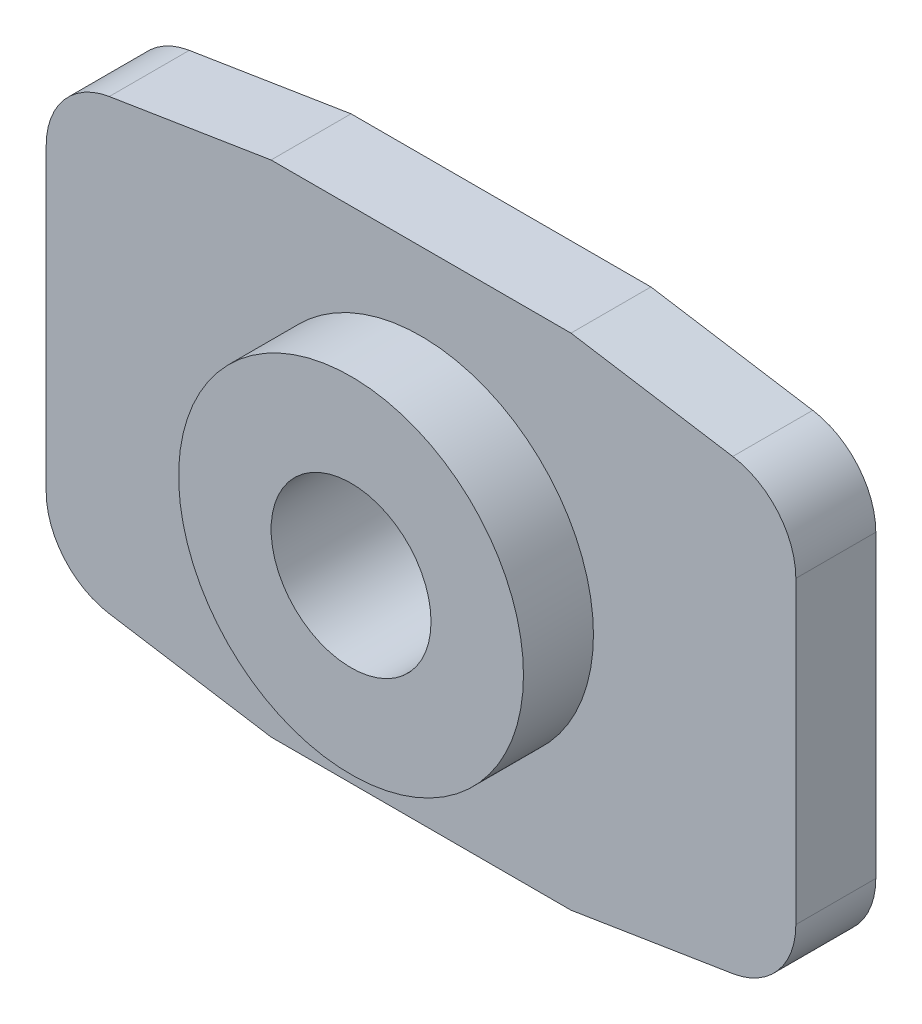
SolidWorks part; units mm, degrees
material "Plain Carbon Steel"
ref_plane "Front Plane" through (0, 0, 0) normal (0, 0, 1) x (1, 0, 0)
ref_plane "Top Plane" through (0, 0, 0) normal (0, 1, 0) x (1, 0, 0)
ref_plane "Right Plane" through (0, 0, 0) normal (1, 0, 0) x (0, 0, -1)
sketch "Sketch1" plane through (0, 0, 0) normal (0, 0, 1) x (1, 0, 0)
  line L0 (-7.5, 0) -> (7.5, 0) construction
  line L1 (-6.2374, 4.4811) -> (-3, 5)
  line L2 (-7.5, -3) -> (-7.5, 3)
  line L3 (-3, 5) -> (3, 5)
  line L4 (7.5, -3) -> (7.5, 3)
  line L5 (0, 5) -> (0, 0) construction
  line L6 (6.2374, 4.4811) -> (3, 5)
  line L7 (6.2374, -4.4811) -> (3, -5)
  line L8 (-3, -5) -> (3, -5)
  line L9 (-6.2374, -4.4811) -> (-3, -5)
  arc A0 (7.5, 3) -> (6.2374, 4.4811) centre (6, 3) ccw
  arc A1 (-7.5, -3) -> (-6.2374, -4.4811) centre (-6, -3) ccw
  arc A2 (7.5, -3) -> (6.2374, -4.4811) centre (6, -3) cw
  arc A3 (-7.5, 3) -> (-6.2374, 4.4811) centre (-6, 3) cw
  dimension "D3" = 6
  dimension "D5" = 1.5
  dimension "D1" = 15
  dimension "D2" = 10
  dimension "D4" = 6
extrude "Boss-Extrude1" add sketch "Sketch1" along normal blind 1.6
sketch "Sketch2" plane through (0, 0, 1.6) normal (0, 0, 1) x (1, 0, 0)
  line L0 (-7.5, 0) -> (0, 0) construction
  line L1 (-7.5, 3) -> (-7.5, -3) construction
  line L2 (0, 0) -> (0, 5) construction
  line L4 (3, 5) -> (-3, 5) construction
  circle A0 centre (0, 0) radius 3.45
  dimension "D2" = 6.9
extrude "Boss-Extrude2" add sketch "Sketch2" along normal blind 1.4
hole_wizard "M5x0.8 Tapped Hole1" positions "Sketch4" profile "Sketch3" tap size "M5x0.8" standard "ANSI Metric" end condition through all
sketch "Sketch4" plane through (0, 0, 3) normal (0, 0, 1) x (1, 0, 0)
  point P0 (0, 0)
sketch "Sketch3" plane through (0, 0, 3) normal (1, 0, 0) x (0, -1, 0)
  line L0 (0, 0) -> (0, 3)
  line L1 (0, 3) -> (1.6, 3)
  line L2 (1.6, 3) -> (1.6, 0)
  line L5 (1.6, 0) -> (0, 0)
  line L11 (0, -6.35) -> (0, 107.95) construction
  dimension "Thread Major Dia." = 3.2
  dimension "Thru Tap Drill Depth" = 3
